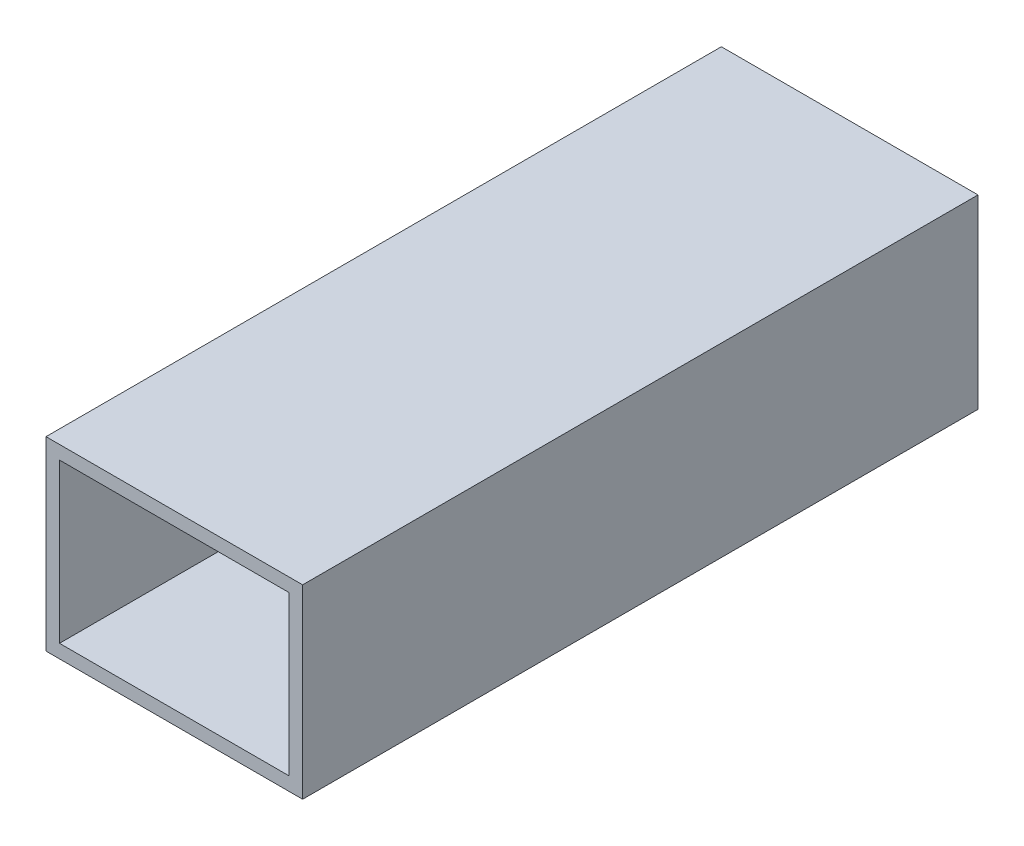
SolidWorks part; units mm, degrees
material "6061 Alloy"
ref_plane "Front Plane" through (0, 0, 0) normal (0, 0, 1) x (1, 0, 0)
ref_plane "Top Plane" through (0, 0, 0) normal (0, 1, 0) x (1, 0, 0)
ref_plane "Right Plane" through (0, 0, 0) normal (1, 0, 0) x (0, 0, -1)
sketch "Sketch1" plane through (0, 0, 0) normal (0, 0, 1) x (1, 0, 0)
  line L1 (-17.1253, 14.6067) -> (20.8747, 14.6067)
  line L2 (-17.1253, 14.6067) -> (-17.1253, -12.8933)
  line L3 (-17.1253, -12.8933) -> (20.8747, -12.8933)
  line L4 (20.8747, 14.6067) -> (20.8747, -12.8933)
  line L5 (-15.1253, 12.6067) -> (18.8747, 12.6067)
  line L6 (-15.1253, 12.6067) -> (-15.1253, -10.8933)
  line L7 (-15.1253, -10.8933) -> (18.8747, -10.8933)
  line L8 (18.8747, 12.6067) -> (18.8747, -10.8933)
  dimension "D1" = 38
  dimension "D2" = 27.5
  dimension "D3" = 23.5
  dimension "D4" = 2
  dimension "D5" = 2
  dimension "D6" = 2
extrude "Boss-Extrude1" add sketch "Sketch1" along normal blind 100
